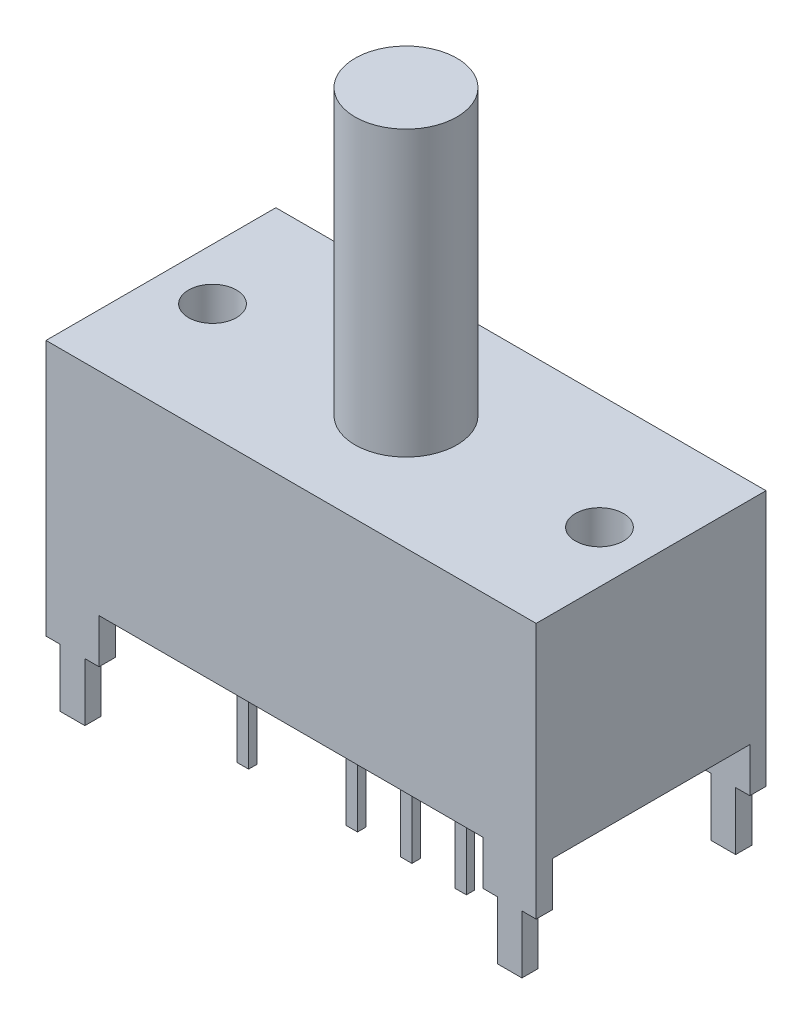
SolidWorks part; units mm, degrees
ref_plane "Front Plane" through (0, 0, 0) normal (0, 0, 1) x (1, 0, 0)
ref_plane "Top Plane" through (0, 0, 0) normal (0, 1, 0) x (1, 0, 0)
ref_plane "Right Plane" through (0, 0, 0) normal (1, 0, 0) x (0, 0, -1)
sketch "Sketch1" plane through (0, 0, 0) normal (0, 1, 0) x (1, 0, 0)
  line L1 (11.55, 5.4166) -> (-11.55, 5.4165)
  line L2 (11.55, 5.4166) -> (11.55, -5.4165)
  line L3 (11.55, -5.4165) -> (-11.55, -5.4166)
  line L4 (-11.55, 5.4165) -> (-11.55, -5.4166)
  line L5 (11.55, 5.4166) -> (-11.55, -5.4166) construction
  line L6 (11.55, -5.4165) -> (-11.55, 5.4165) construction
  point P0 (0, 0)
  dimension "D1" = 23.1
  dimension "D2" = 10.8331
extrude "Boss-Extrude1" add sketch "Sketch1" along normal blind 9.9822
sketch "Sketch2" plane through (0, 0, 0) normal (0, -1, 0) x (1, 0, 0)
  line L0 (0, 0) -> (11.55, 0) construction
  line L1 (11.55, -5.4166) -> (9.0481, -5.4166)
  line L2 (11.55, -5.4166) -> (11.55, -4.6546)
  line L3 (11.55, -4.6546) -> (9.0481, -4.6546)
  line L4 (9.0481, -5.4166) -> (9.0481, -4.6546)
  line L5 (11.55, 5.4165) -> (11.55, -5.4166) construction
  line L6 (0, 0) -> (0, 5.4165) construction
  line L7 (-11.55, 5.4166) -> (11.55, 5.4165) construction
  line L8 (9.0481, 5.4166) -> (9.0481, 4.6546)
  line L9 (11.55, 4.6546) -> (9.0481, 4.6546)
  line L10 (11.55, 5.4166) -> (11.55, 4.6546)
  line L11 (11.55, 5.4166) -> (9.0481, 5.4166)
  line L12 (-11.55, 5.4166) -> (-9.0481, 5.4166)
  line L13 (-11.55, 5.4166) -> (-11.55, 4.6546)
  line L14 (-11.55, 4.6546) -> (-9.0481, 4.6546)
  line L15 (-9.0481, 5.4166) -> (-9.0481, 4.6546)
  line L16 (-9.0481, -5.4166) -> (-9.0481, -4.6546)
  line L17 (-11.55, -4.6546) -> (-9.0481, -4.6546)
  line L18 (-11.55, -5.4166) -> (-11.55, -4.6546)
  line L19 (-11.55, -5.4166) -> (-9.0481, -5.4166)
  dimension "D1" = 2.5019
  dimension "D2" = 0.762
extrude "Boss-Extrude2" add sketch "Sketch2" along normal blind 4.826
sketch "Sketch3" plane through (0, 0, 0) normal (0, -1, 0) x (1, 0, 0)
  line L0 (11.55, 4.6545) -> (11.55, -4.6546) construction
  line L1 (5.5429, -2.775) -> (4.9968, -2.775)
  line L2 (5.5429, -2.775) -> (5.5429, -2.3813)
  line L3 (5.5429, -2.3813) -> (4.9968, -2.3813)
  line L4 (4.9968, -2.775) -> (4.9968, -2.3813)
  line L5 (9.0481, -5.4166) -> (-9.0481, -5.4166) construction
  dimension "D1" = 0.3937
  dimension "D2" = 0.5461
  dimension "D3" = 6.0071
  dimension "D4" = 2.6416
extrude "Boss-Extrude3" add sketch "Sketch3" along normal blind 5.461
pattern_linear "LPattern1" count 5 spacing 2.5654 along (-1, 0, 0) count 2 spacing 5.08 along (0, 0, 1) skipping (3, 0), (3, 1) of "Boss-Extrude3"
sketch "Sketch4" plane through (0, 9.9822, 0) normal (0, 1, 0) x (1, 0, 0)
  circle A0 centre (0, 0) radius 2.4003
  dimension "D1" = 4.8006
extrude "Boss-Extrude4" add sketch "Sketch4" along normal blind 13.3858
sketch "Sketch5" plane through (0, 9.9822, 0) normal (0, 1, 0) x (1, 0, 0)
  line L0 (0, 0) -> (0, -5.4165) construction
  line L1 (-11.55, -5.4166) -> (11.55, -5.4165) construction
  line L2 (0, 0) -> (9.1186, 0) construction
  line L3 (11.55, -5.4165) -> (11.55, 5.4166) construction
  circle A0 centre (9.1186, 0) radius 1.1303
  circle A1 centre (-9.1186, 0) radius 1.1303
  dimension "D1" = 2.2606
  dimension "D2" = 18.2372
  dimension "D3" = 2.4314
extrude "Cut-Extrude1" cut sketch "Sketch5" against normal blind 2.54
sketch "Sketch6" plane through (0, 0, -5.4166) normal (0, 0, -1) x (-1, 0, 0)
  line L0 (-11.55, 9.9822) -> (11.55, 9.9822) construction
  line L1 (-11.55, -4.826) -> (-10.8809, -4.826)
  line L2 (-11.55, -4.826) -> (-11.55, -2.0878)
  line L3 (-11.55, -2.0878) -> (-10.8809, -2.0878)
  line L4 (-10.8809, -4.826) -> (-10.8809, -2.0878)
  line L5 (-9.0481, -4.826) -> (-9.7172, -4.826)
  line L6 (-9.0481, -4.826) -> (-9.0481, -2.0878)
  line L7 (-9.0481, -2.0878) -> (-9.7172, -2.0878)
  line L8 (-9.7172, -4.826) -> (-9.7172, -2.0878)
  line L9 (9.0481, -4.826) -> (9.7172, -4.826)
  line L10 (9.0481, -4.826) -> (9.0481, -2.0878)
  line L11 (9.0481, -2.0878) -> (9.7172, -2.0878)
  line L12 (9.7172, -4.826) -> (9.7172, -2.0878)
  line L13 (11.55, -4.826) -> (10.8809, -4.826)
  line L14 (11.55, -4.826) -> (11.55, -2.0878)
  line L15 (11.55, -2.0878) -> (10.8809, -2.0878)
  line L16 (10.8809, -4.826) -> (10.8809, -2.0878)
  dimension "D1" = 12.07
extrude "Cut-Extrude2" cut sketch "Sketch6" against normal through all both and the other way through all
